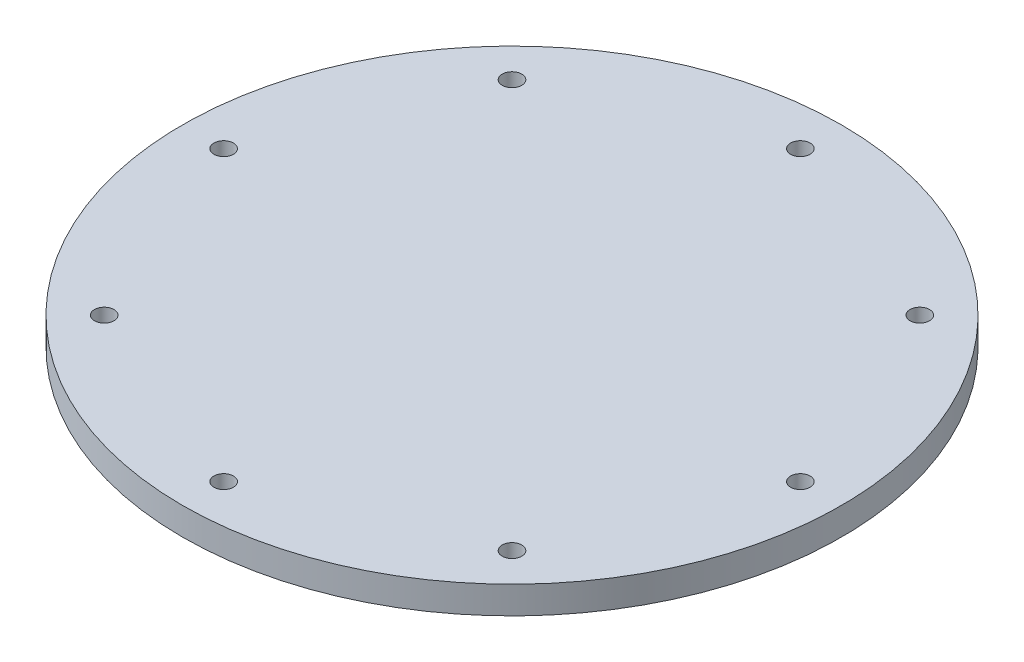
SolidWorks part; units mm, degrees
ref_plane "Front Plane" through (0, 0, 0) normal (0, 0, 1) x (1, 0, 0)
ref_plane "Top Plane" through (0, 0, 0) normal (0, 1, 0) x (1, 0, 0)
ref_plane "Right Plane" through (0, 0, 0) normal (1, 0, 0) x (0, 0, -1)
sketch "Sketch1" plane through (0, 0, 0) normal (0, 1, 0) x (1, 0, 0)
  circle A0 centre (0, 0) radius 38.1
  dimension "D1" = 76.2
extrude "Boss-Extrude1" add sketch "Sketch1" along normal blind 3.175
hole_wizard "Tap Drill for #4-40 Tap1" positions "Sketch3" profile "Sketch4" hole size "#4-40" standard "ANSI Inch" end condition through all
sketch "Sketch3" plane through (0, 0, 0) normal (0, -1, 0) x (-1, 0, 0)
  point P0 (0, -33.3375)
  dimension "D1" = 33.3375
sketch "Sketch4" plane through (0, 0, 33.3375) normal (1, 0, 0) x (0, 0, -1)
  line L0 (0, 0) -> (0, 3.175)
  line L1 (0, 3.175) -> (1.1303, 3.175)
  line L2 (1.1303, 3.175) -> (1.1303, 0)
  line L5 (1.1303, 0) -> (0, 0)
  line L11 (0, -6.35) -> (0, 107.95) construction
  dimension "Thru Hole Dia." = 2.2606
  dimension "Thru Hole Depth" = 3.175
pattern_circular "CirPattern1" count 8 over 360 about axis through (0, 0, 0) along (0, 1, 0) of "Tap Drill for #4-40 Tap1"
